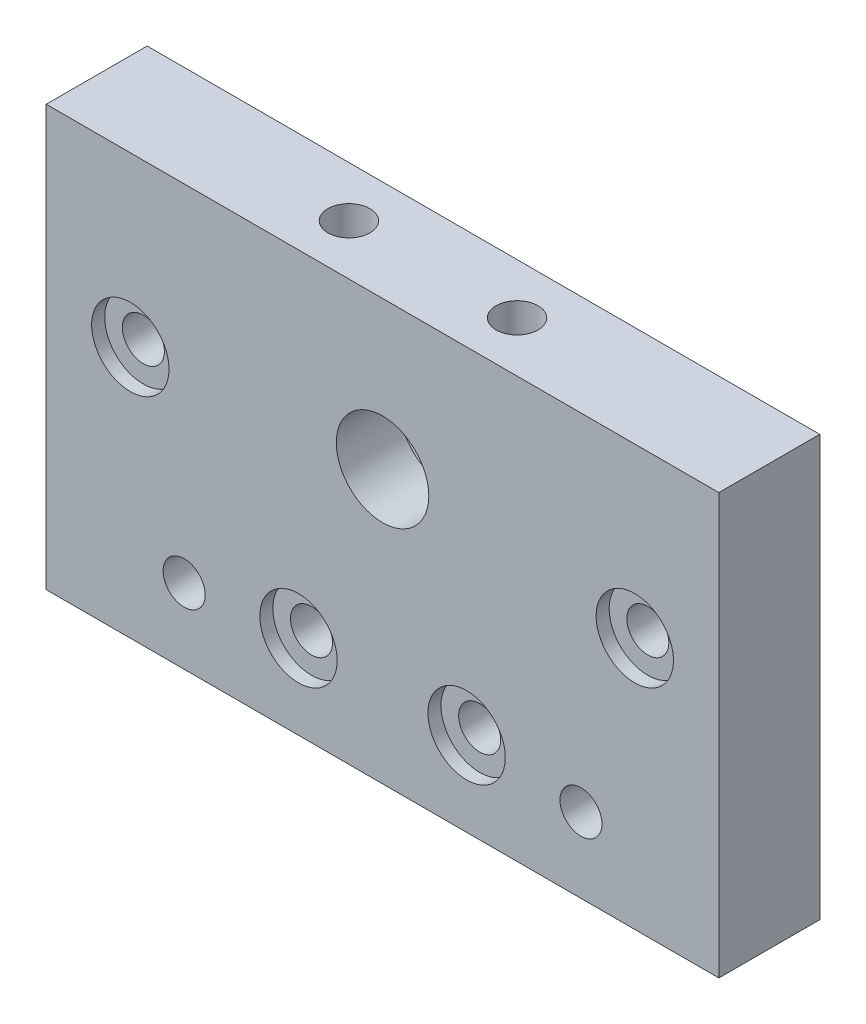
SolidWorks part; units mm, degrees
ref_plane "Front" through (0, 0, 0) normal (0, 0, 1) x (1, 0, 0)
ref_plane "Top" through (0, 0, 0) normal (0, 1, 0) x (1, 0, 0)
ref_plane "Right" through (0, 0, 0) normal (1, 0, 0) x (0, 0, -1)
sketch "Sketch1" plane through (0, 0, 0) normal (0, 0, 1) x (1, 0, 0)
  line L0 (40, 0) -> (40, 50) construction
  line L1 (0, 0) -> (80, 0)
  line L2 (0, 0) -> (0, 50)
  line L3 (0, 50) -> (80, 50)
  line L4 (80, 0) -> (80, 50)
  line L5 (0, 32.4) -> (80, 32.4) construction
  line L6 (0, 30) -> (80, 30) construction
  line L7 (0, 10) -> (80, 10) construction
  line L8 (0, 8.9) -> (80, 8.9) construction
  circle A0 centre (40, 32.4) radius 5.5
  circle A1 centre (10, 30) radius 2.5
  circle A2 centre (70, 30) radius 2.5
  circle A3 centre (30, 10) radius 2.5
  circle A4 centre (50, 10) radius 2.5
  circle A5 centre (16.4, 8.9) radius 2.5
  circle A6 centre (63.6, 8.9) radius 2.5
  point P9 (40, 32.4)
  dimension "D3" = 11
  dimension "D6" = 5
  dimension "D9" = 5
  dimension "D12" = 5
  dimension "D1" = 80
  dimension "D2" = 50
  dimension "D4" = 17.6
  dimension "D5" = 30
  dimension "D7" = 10
  dimension "D8" = 30
  dimension "D10" = 10
  dimension "D11" = 8.9
  dimension "D13" = 16.4
extrude "Boss-Extrude1" add sketch "Sketch1" along normal blind 12
sketch "Sketch2" plane through (0, 0, 12) normal (0, 0, 1) x (1, 0, 0)
  line L0 (40, 50) -> (40, 0) construction
  line L1 (80, 50) -> (0, 50) construction
  line L2 (0, 0) -> (80, 0) construction
  circle A0 centre (10, 30) radius 4.6
  circle A1 centre (70, 30) radius 4.6
  circle A2 centre (30, 10) radius 4.6
  circle A3 centre (50, 10) radius 4.6
  dimension "D1" = 9.2
  dimension "D2" = 9.2
extrude "Cut-Extrude1" cut sketch "Sketch2" against normal blind 1.55
sketch "Sketch3" plane through (0, 0, 0) normal (0, 0, -1) x (-1, 0, 0)
  circle A0 centre (-40, 32.4) radius 8.05
  dimension "D1" = 16.1
extrude "Cut-Extrude2" cut sketch "Sketch3" against normal blind 4.5
sketch "Sketch4" plane through (0, 50, 0) normal (0, 1, 0) x (1, 0, 0)
  line L0 (80, -6) -> (0, -6) construction
  line L1 (80, -12) -> (80, 0) construction
  line L2 (0, -12) -> (0, 0) construction
  line L3 (40, -12) -> (40, 0) construction
  line L4 (80, -12) -> (0, -12) construction
  line L5 (80, 0) -> (0, 0) construction
  circle A0 centre (50, -6) radius 2.5
  circle A1 centre (30, -6) radius 2.5
  dimension "D2" = 5
  dimension "D1" = 15
extrude "Cut-Extrude3" cut sketch "Sketch4" against normal blind 11
